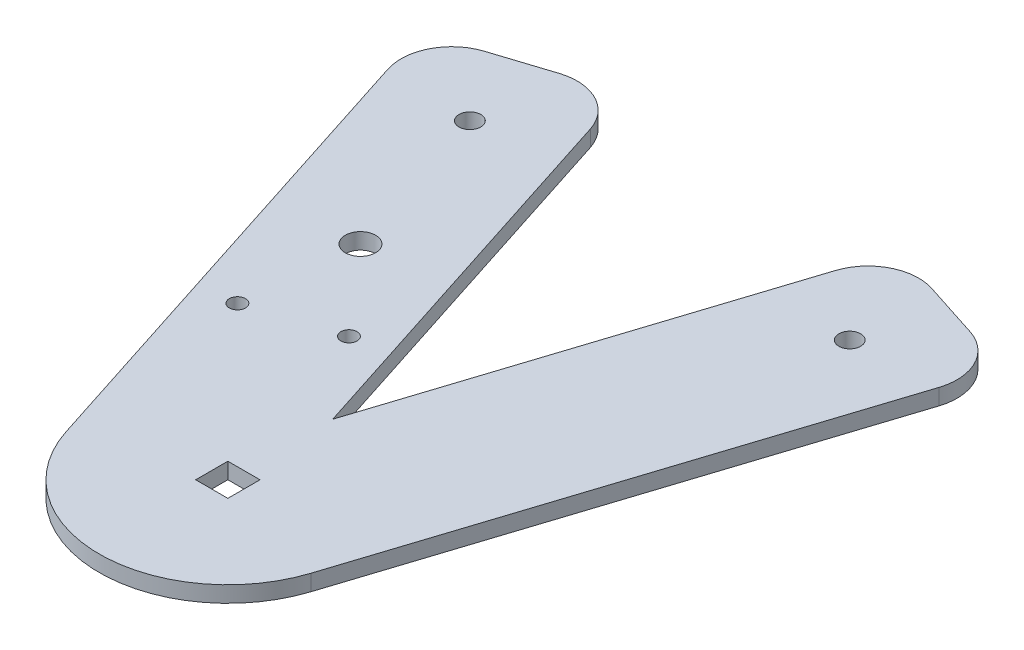
SolidWorks part; units mm, degrees
ref_plane "Front Plane" through (0, 0, 0) normal (0, 0, 1) x (1, 0, 0)
ref_plane "Top Plane" through (0, 0, 0) normal (0, 1, 0) x (1, 0, 0)
ref_plane "Right Plane" through (0, 0, 0) normal (1, 0, 0) x (0, 0, -1)
sketch "Sketch1" plane through (0, 0, 0) normal (0, 1, 0) x (1, 0, 0)
  line L0 (-37.5, 85.2955) -> (37.5, 85.2955) construction
  line L1 (-3.175, -3.175) -> (3.175, -3.175)
  line L2 (-3.175, -3.175) -> (-3.175, 3.175)
  line L3 (-3.175, 3.175) -> (3.175, 3.175)
  line L4 (3.175, -3.175) -> (3.175, 3.175)
  line L5 (-3.175, -3.175) -> (3.175, 3.175) construction
  line L6 (-3.175, 3.175) -> (3.175, -3.175) construction
  line L7 (-57.4796, 95.535) -> (-24.1752, -7.7922)
  line L8 (24.1752, -7.7922) -> (57.4796, 95.535)
  line L9 (-27.2606, 105.2752) -> (0, 20.699)
  line L10 (0, 20.699) -> (27.2606, 105.2752)
  line L11 (27.2606, 105.2752) -> (57.4796, 95.535)
  line L12 (-57.4796, 95.535) -> (-27.2606, 105.2752)
  line L13 (-44.9684, 108.4662) -> (-30.1134, 62.3786) construction
  line L14 (-2.364, -38.3829) -> (15336.5326, 47550.6731) construction
  line L15 (-29.2314, 31.1199) -> (-12.5752, 36.4885) construction
  circle A0 centre (37.5, 85.2955) radius 2.15
  circle A1 centre (-37.5, 85.2955) radius 2.15
  arc A2 (24.1752, -7.7922) -> (-24.1752, -7.7922) centre (0, 0) cw
  circle A3 centre (-27.2229, 53.4109) radius 3
  circle A4 centre (-29.2314, 31.1199) radius 1.6
  circle A5 centre (-12.5752, 36.4885) radius 1.6
  point P4 (0, 0)
  point P10 (0, 85.2955)
  point P19 (42.3701, 100.4051)
  point P20 (-42.3701, 100.4051)
  point P31 (-20.9033, 33.8042)
  dimension "D3" = 4.3
  dimension "D7" = 25.4
  dimension "D8" = 6
  dimension "D9" = 33.5
  dimension "D11" = 3.2
  dimension "D1" = 6.35
  dimension "D2" = 31.75
  dimension "D4" = 93.175
  dimension "D5" = 75
  dimension "D6" = 15.875
  dimension "D10" = 17.5
  dimension "D12" = 20.6
extrude "Boss-Extrude1" add sketch "Sketch1" along normal blind 3.175
fillet "Fillet1" radius 10 4 edges at (57.4796, 1.5875, -95.535) (27.2606, 1.5875, -105.2752) (-27.2606, 1.5875, -105.2752) (-57.4796, 1.5875, -95.535)
